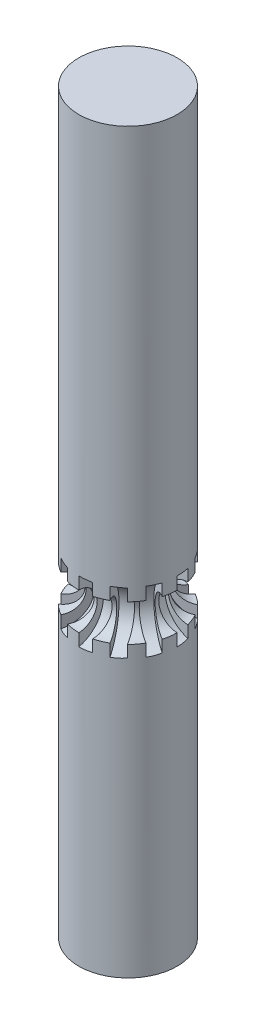
SolidWorks part; units mm, degrees
ref_plane "Plan de face" through (0, 0, 0) normal (0, 0, 1) x (1, 0, 0)
ref_plane "Plan de dessus" through (0, 0, 0) normal (0, 1, 0) x (1, 0, 0)
ref_plane "Plan de droite" through (0, 0, 0) normal (1, 0, 0) x (0, 0, -1)
sketch "Esquisse1" plane through (0, 0, 0) normal (0, 1, 0) x (1, 0, 0)
  circle A0 centre (0, 0) radius 4
  dimension "D1" = 8
extrude "Boss.-Extru.1" add sketch "Esquisse1" along normal blind 60
cosmetic thread "Représentation de filetage1" parameters "D1"=15, "D2"=6.891
cosmetic thread "Représentation de filetage2" parameters "D1"=15, "D2"=6.891
ref_plane "Plan1" through (0, 25, 0) normal (0, 1, 0) x (1, 0, 0)
sketch "Esquisse3" plane through (0, 25, 0) normal (0, 1, 0) x (1, 0, 0)
  circle A0 centre (0, 0) radius 4
  dimension "D1" = 8
sketch "Esquisse4" plane through (0, 0, 0) normal (0, 0, 1) x (1, 0, 0)
  line L0 (4, 0) -> (4, 60) construction
  line L1 (4.4, 25) -> (-4.4, 25) construction
  line L2 (4, 27.5) -> (4, 22.5)
  arc A0 (4, 27.5) -> (4, 22.5) centre (4.5625, 25) ccw
  point P7 (2, 25)
  dimension "D1" = 5
  dimension "D2" = 2
extrude "Enlèv. mat.-Extru.2" cut sketch "Esquisse4" against normal blind 1
pattern_curve "Répét. par courbe1" of "Enlèv. mat.-Extru.2" parameters "D1"=12, "D3"=1.5, "D2"=1, "D4"=1
sketch "Esquisse5" plane through (0, 0, 0) normal (1, 0, 0) x (0, 0, -1)
  line L0 (-4, 22.5) -> (-4, 27.5) construction
  circle A0 centre (-4, 25) radius 1.5
  dimension "D1" = 3
sweep "Enlèvement de matière-Balayage1" cut profiles "Esquisse5" path "Esquisse3"
